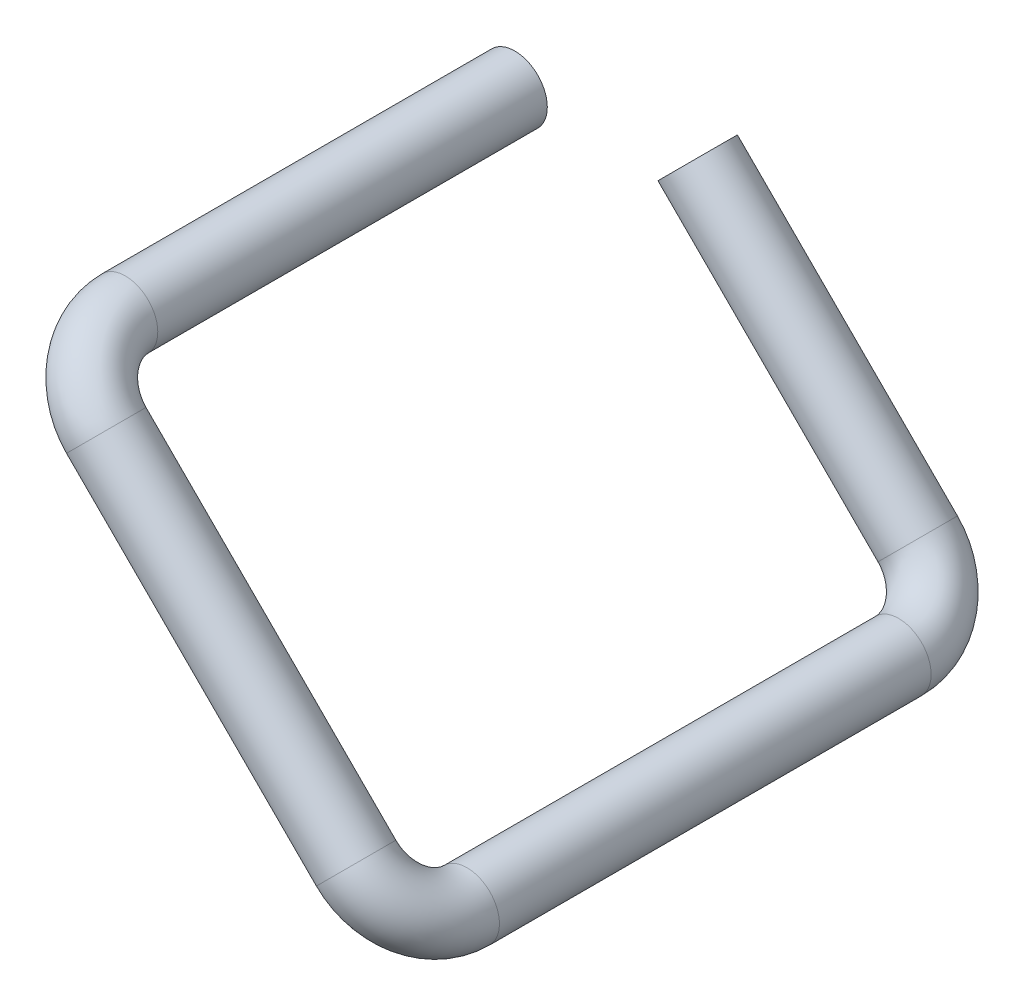
SolidWorks part; units mm, degrees
ref_plane "Front" through (0, 0, 0) normal (0, 0, 1) x (1, 0, 0)
ref_plane "Top" through (0, 0, 0) normal (0, 1, 0) x (1, 0, 0)
ref_plane "Side" through (0, 0, 0) normal (1, 0, 0) x (0, 0, -1)
sketch "PipeSketch" plane through (0, 0, 0) normal (0, 0, 1) x (1, 0, 0)
  circle A0 centre (0, 0) radius 6.35
  circle A1 centre (0, 0) radius 5.842 construction
  dimension "OuterDiameter" = 12.7
  dimension "InnerDiameter" = 11.684
sketch "FilterSketch" plane through (0, 0, 0) normal (0, 0, 1) x (1, 0, 0)
  circle A0 centre (0, 0) radius 6.35 construction
  dimension "NominalDiameter" = 12.7
sketch3d "3DSketch1"
  line L0 (0, 0, 10) -> (0, 0, 76.2004) construction
  line L1 (8.9803, -8.9803, 88.9004) -> (57.8581, -57.8581, 88.9004) construction
  line L2 (66.8384, -66.8384, -8.2499) -> (66.8384, -66.8384, 76.2004) construction
  line L3 (21.8849, -21.8849, -20.9499) -> (57.8581, -57.8581, -20.9499) construction
  line L4 (0, 0, 0) -> (0, 0, 76.2004)
  line L5 (8.9803, -8.9803, 88.9004) -> (57.8581, -57.8581, 88.9004)
  line L6 (66.8384, -66.8384, -8.2499) -> (66.8384, -66.8384, 76.2004)
  line L7 (14.8138, -14.8138, -20.9499) -> (57.8581, -57.8581, -20.9499)
  arc A0 (8.9803, -8.9803, 88.9004) -> (0, 0, 76.2004) centre (8.9803, -8.9803, 76.2004) ccw construction
  arc A1 (66.8384, -66.8384, 76.2004) -> (57.8581, -57.8581, 88.9004) centre (57.8581, -57.8581, 76.2004) ccw construction
  arc A2 (57.8581, -57.8581, -20.9499) -> (66.8384, -66.8384, -8.2499) centre (57.8581, -57.8581, -8.2499) ccw construction
  arc A3 (8.9803, -8.9803, 88.9004) -> (0, 0, 76.2004) centre (8.9803, -8.9803, 76.2004) ccw
  arc A4 (66.8384, -66.8384, 76.2004) -> (57.8581, -57.8581, 88.9004) centre (57.8581, -57.8581, 76.2004) ccw
  arc A5 (57.8581, -57.8581, -20.9499) -> (66.8384, -66.8384, -8.2499) centre (57.8581, -57.8581, -8.2499) ccw
  point P5 (0, -17.9605, 76.2004)
  point P6 (0, -17.9605, 76.2004)
  point P7 (48.8779, -66.8384, 76.2004)
  point P11 (48.8779, -66.8384, -8.2499)
  point P12 (48.8779, -66.8384, 76.2004)
  point P18 (48.8779, -66.8384, -8.2499)
sweep "ThinSweep" add profiles "PipeSketch" path "3DSketch1" parameters "WallThickness"=0.508
ref_plane "Plane1" through (0, 0, 0) normal (0, 0, 1) x (1, 0, 0)
